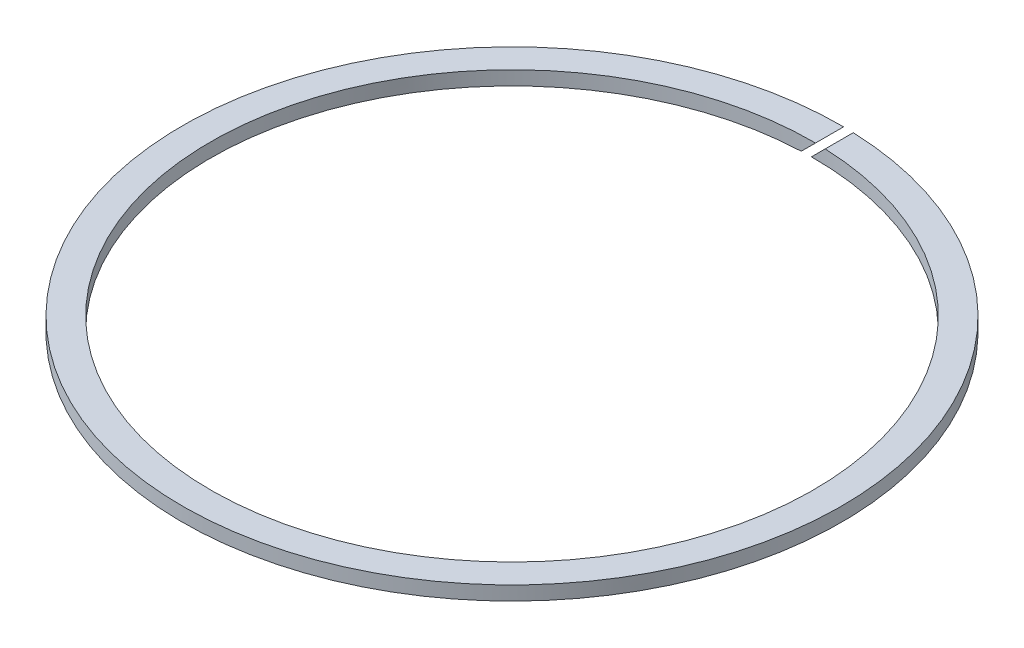
SolidWorks part; units mm, degrees
ref_plane "Front Plane" through (0, 0, 0) normal (0, 0, 1) x (1, 0, 0)
ref_plane "Top Plane" through (0, 0, 0) normal (0, 1, 0) x (1, 0, 0)
ref_plane "Right Plane" through (0, 0, 0) normal (1, 0, 0) x (0, 0, -1)
sketch "Sketch1" plane through (0, 0, 0) normal (0, 1, 0) x (1, 0, 0)
  circle A0 centre (0, 0) radius 43
  circle A1 centre (0, 0) radius 47
  dimension "D1" = 94
  dimension "D2" = 86
extrude "Boss-Extrude1" add sketch "Sketch1" along normal mid plane 2
sketch "Sketch2" plane through (0, 0, 0) normal (0, 0, 1) x (1, 0, 0)
  line L0 (-7.4246, -6.7175) -> (6.7175, 7.4246)
  line L1 (-7.4246, -6.7175) -> (-6.7175, -7.4246)
  line L2 (6.7175, 7.4246) -> (7.4246, 6.7175)
  line L3 (-6.7175, -7.4246) -> (7.4246, 6.7175)
  line L4 (-7.4246, -6.7175) -> (7.4246, 6.7175) construction
  line L5 (6.7175, 7.4246) -> (-6.7175, -7.4246) construction
  line L6 (47, 1) -> (-47, 1) construction
  point P1 (0, 0)
  dimension "D1" = 1
  dimension "D2" = 45
  dimension "D3" = 20
extrude "Cut-Extrude1" cut sketch "Sketch2" against normal through all
